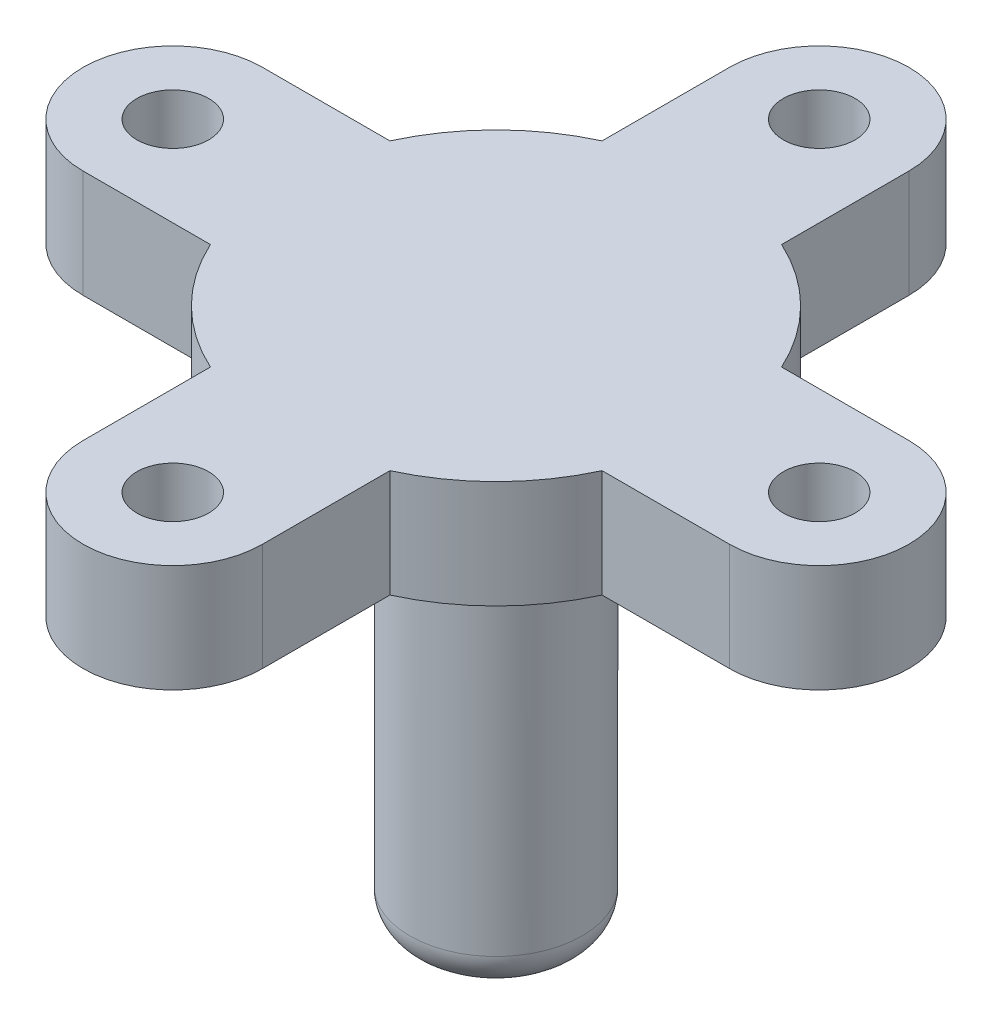
SolidWorks part; units mm, degrees
ref_plane "Front Plane" through (0, 0, 0) normal (0, 0, 1) x (1, 0, 0)
ref_plane "Top Plane" through (0, 0, 0) normal (0, 1, 0) x (1, 0, 0)
ref_plane "Right Plane" through (0, 0, 0) normal (1, 0, 0) x (0, 0, -1)
sketch "Sketch1" plane through (0, 0, 0) normal (0, 1, 0) x (1, 0, 0)
  line L0 (0, 45.0113) -> (0, 30) construction
  line L1 (7.5, 45.0113) -> (-7.5, 45.0113) construction
  line L2 (12.5, 45.0113) -> (12.5, 27.2718)
  line L3 (-12.5, 45) -> (-12.5, 27.2718)
  line L4 (45.0113, -12.5) -> (27.2718, -12.5)
  line L5 (45, 12.5) -> (27.2718, 12.5)
  line L7 (-12.5, -45.0113) -> (-12.5, -27.2718)
  line L8 (12.5, -45) -> (12.5, -27.2718)
  line L10 (-45.0113, 12.5) -> (-27.2718, 12.5)
  line L11 (-45, -12.5) -> (-27.2718, -12.5)
  line L13 (-45, 0) -> (-40, 0) construction
  line L14 (0, -40) -> (0, -30) construction
  line L15 (45, 0) -> (40, 0) construction
  arc A0 (-12.5, 27.2718) -> (-27.2718, 12.5) centre (0, 0) ccw
  arc A1 (12.5, 45.0113) -> (-12.5, 45) centre (0, 45.0113) ccw
  circle A4 centre (0, 45.0113) radius 5
  arc A5 (45.0113, -12.5) -> (45, 12.5) centre (45.0113, 0) ccw
  circle A6 centre (45.0113, 0) radius 5
  arc A7 (-12.5, -45.0113) -> (12.5, -45) centre (0, -45.0113) ccw
  circle A8 centre (0, -45.0113) radius 5
  arc A9 (-45.0113, 12.5) -> (-45, -12.5) centre (-45.0113, 0) ccw
  circle A10 centre (-45.0113, 0) radius 5
  arc A11 (27.2718, 12.5) -> (12.5, 27.2718) centre (0, 0) ccw
  arc A12 (12.5, -27.2718) -> (27.2718, -12.5) centre (0, 0) ccw
  arc A13 (-27.2718, -12.5) -> (-12.5, -27.2718) centre (0, 0) ccw
  point P40 (0, 0)
  dimension "D1" = 60
  dimension "D2" = 10
  dimension "D3" = 25
  dimension "D4" = 4
extrude "Boss-Extrude1" add sketch "Sketch1" along normal mid plane 15
sketch "Sketch2" plane through (0, -7.5, 0) normal (0, -1, 0) x (1, 0, 0)
  circle A0 centre (0, 0) radius 12
  dimension "D1" = 24
extrude "Boss-Extrude2" add sketch "Sketch2" along normal blind 60
fillet "Fillet1" radius 5 2 edges at (0, -7.5, 12) (0, -67.5, -12)
scale "Scale1" scale about centroid uniform scaling yes scale factor 0.6
